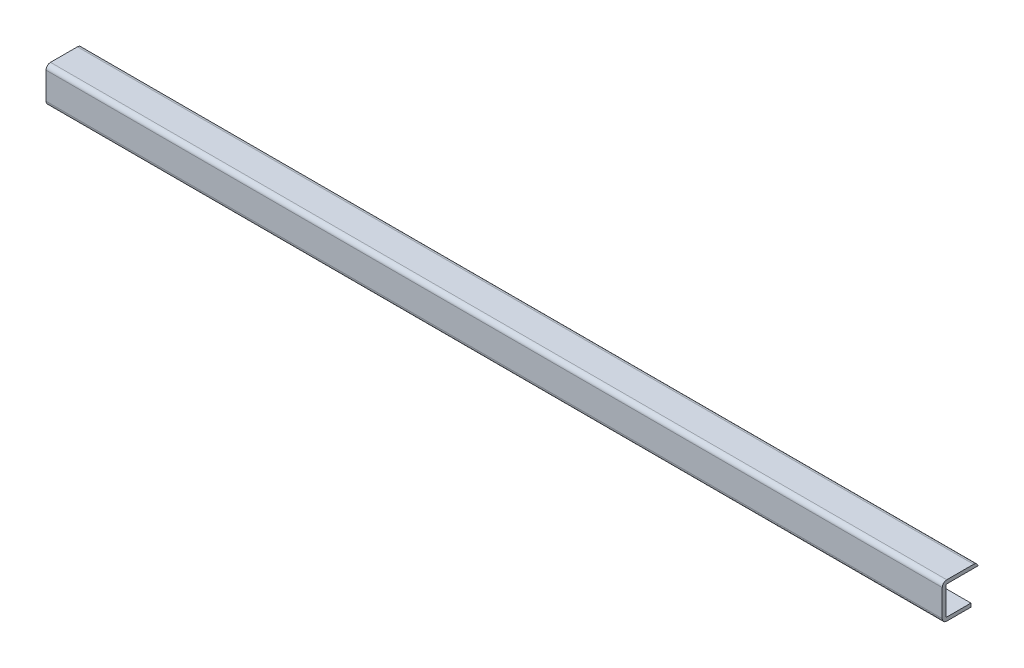
SolidWorks part; units mm, degrees
ref_plane "Спереди" through (0, 0, 0) normal (0, 0, 1) x (1, 0, 0)
ref_plane "Сверху" through (0, 0, 0) normal (0, 1, 0) x (1, 0, 0)
ref_plane "Справа" through (0, 0, 0) normal (1, 0, 0) x (0, 0, -1)
sketch "Эскиз1" plane through (0, 0, 0) normal (1, 0, 0) x (0, 0, -1)
  line L5 (1, 0) -> (31, 0)
  line L6 (0, 1) -> (0, 31)
  line L7 (1, 32) -> (31, 32)
  line L8 (32, 1) -> (32, 31)
  arc A4 (1, 0) -> (0, 1) centre (1, 1) cw
  arc A5 (31, 0) -> (32, 1) centre (31, 1) ccw
  arc A6 (31, 32) -> (32, 31) centre (31, 31) cw
  arc A7 (1, 32) -> (0, 31) centre (1, 31) ccw
  point P8 (0, 0)
  dimension "D1" = 1
  dimension "D2" = 32
  dimension "32" = 32
extrude "Вытянуть-Тонкостенный1" add sketch "Эскиз1" along normal blind 1000 thin
sketch "Эскиз2" plane through (1000, 0, 0) normal (1, 0, 0) x (0, 0, -1)
  line L0 (31, 32) -> (1, 32) construction
  line L1 (28, 32) -> (36.5554, 32)
  line L2 (28, 32) -> (28, -4.5369)
  line L3 (28, -4.5369) -> (36.5554, -4.5369)
  line L4 (36.5554, 32) -> (36.5554, -4.5369)
  point P6 (36.5554, -4.5369)
  point P7 (0, 0)
extrude "Вырез-Вытянуть1" cut sketch "Эскиз2" against normal through all
